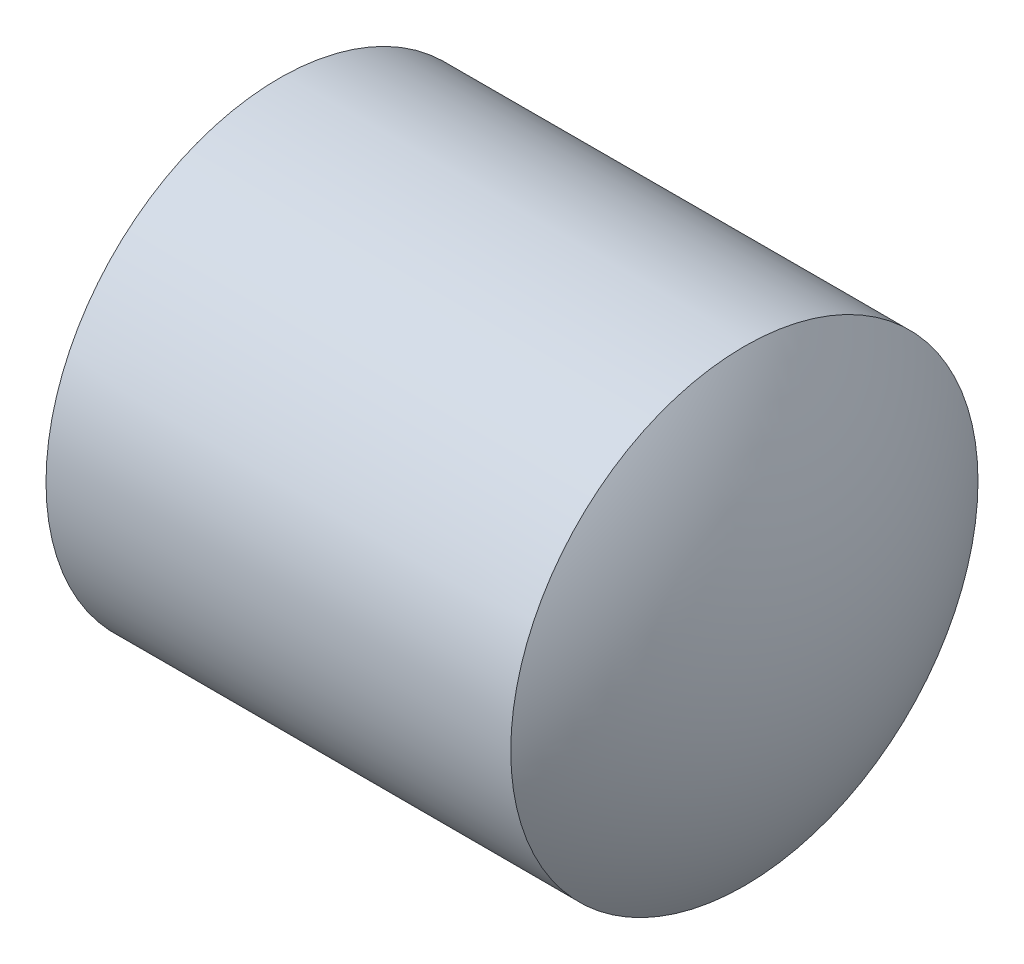
SolidWorks part; units mm, degrees
ref_plane "Front Plane" through (0, 0, 0) normal (0, 0, 1) x (1, 0, 0)
ref_plane "Top Plane" through (0, 0, 0) normal (0, 1, 0) x (1, 0, 0)
ref_plane "Right Plane" through (0, 0, 0) normal (1, 0, 0) x (0, 0, -1)
sketch "Sketch1" plane through (0, 0, 0) normal (0, 1, 0) x (1, 0, 0)
  line L6 (-0.3195, 260.5987) -> (0.6821, 260)
  line L7 (74.3454, 130) -> (323.581, 130) construction
  line L8 (1.3602, 0.3479) -> (0.6821, 260) construction
  line L9 (0.3617, -0.2533) -> (-0.3195, 260.5987) construction
  line L10 (300.4313, 130) -> (301.4313, 130)
  line L11 (259.3179, 260) -> (0.6821, 260)
  line L12 (-0.3195, 260.5987) -> (259.9987, 260.7702)
  arc A2 (259.9987, 260.7702) -> (301.4313, 130) centre (74.3454, 130) cw
  arc A4 (259.3179, 260) -> (300.4313, 130) centre (74.3454, 130) cw
  arc A6 (1.3602, 0.3479) -> (259.6796, 0.5162) centre (130.3617, 243.1974) ccw construction
  arc A7 (0.3617, -0.2533) -> (260.3617, -0.2533) centre (130.3617, 243.1974) ccw construction
  arc A8 (259.3179, 260) -> (259.6796, 0.5162) centre (74.3454, 130) cw construction
  arc A9 (259.9987, 260.7702) -> (260.3617, -0.2533) centre (74.3454, 130) cw construction
  arc A10 (-0.3195, 260.5987) -> (259.9987, 260.7702) centre (130, 17.3189) cw construction
  arc A11 (0.6821, 260) -> (259.3179, 260) centre (130, 17.3189) cw construction
  dimension "D1" = 130
  dimension "D4" = 1
ref_plane "Plane2" through (0, 0, -130) normal (0, 0, 1) x (1, 0, 0)
ref_axis "Axis4" through (61.5048, 0, -130) along (1, 0, 0)
revolve "Revolve9" add sketch "Sketch1" angle 360 about axis through (61.5048, 0, -130) along (1, 0, 0)
